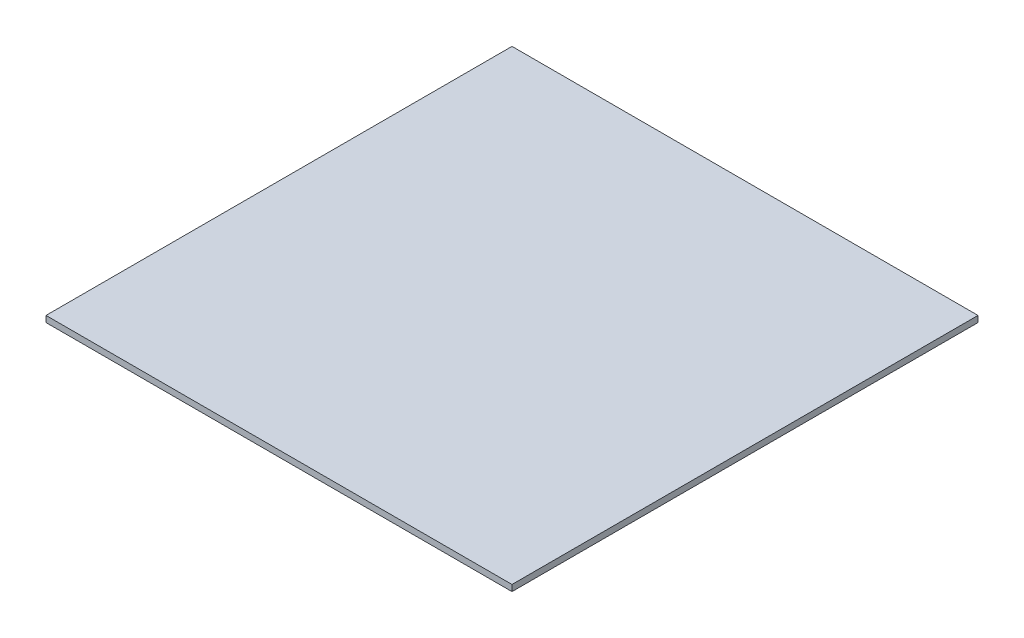
SolidWorks part; units mm, degrees
ref_plane "Front Plane" through (0, 0, 0) normal (0, 0, 1) x (1, 0, 0)
ref_plane "Top Plane" through (0, 0, 0) normal (0, 1, 0) x (1, 0, 0)
ref_plane "Right Plane" through (0, 0, 0) normal (1, 0, 0) x (0, 0, -1)
sketch "Sketch1" plane through (0, 0, 0) normal (0, 1, 0) x (1, 0, 0)
  line L1 (-75, 75) -> (75, 75)
  line L2 (-75, 75) -> (-75, -75)
  line L3 (-75, -75) -> (75, -75)
  line L4 (75, 75) -> (75, -75)
  line L5 (-75, 75) -> (75, -75) construction
  line L6 (-75, -75) -> (75, 75) construction
  point P0 (0, 0)
extrude "Boss-Extrude1" add sketch "Sketch1" along normal blind 2
equation "\"l\"= 15cm'side of the base square"
equation "\"D1@Sketch1\"=\"l\""
